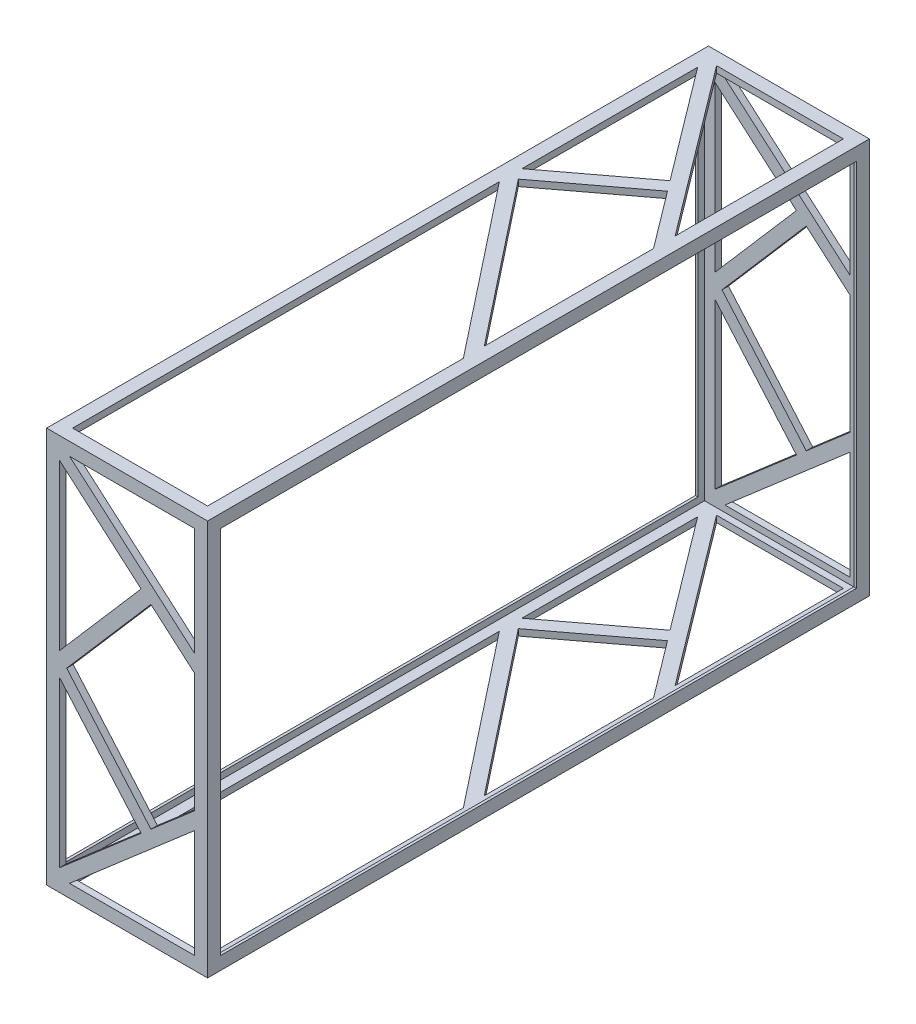
SolidWorks part; units mm, degrees
ref_plane "Front Plane" through (0, 0, 0) normal (0, 0, 1) x (1, 0, 0)
ref_plane "Top Plane" through (0, 0, 0) normal (0, 1, 0) x (1, 0, 0)
ref_plane "Right Plane" through (0, 0, 0) normal (1, 0, 0) x (0, 0, -1)
sketch "Sketch1" plane through (0, 0, 0) normal (1, 0, 0) x (0, 0, -1)
  line L0 (-5, 300) -> (505, 300)
  line L1 (0, 0) -> (500, 0)
  line L2 (0, 0) -> (0, 295)
  line L3 (0, 295) -> (500, 295)
  line L4 (500, 0) -> (500, 295)
  line L5 (505, -5) -> (505, 300)
  line L6 (-5, -5) -> (505, -5)
  line L7 (-5, -5) -> (-5, 300)
  dimension "D1" = 500
  dimension "D2" = 295
  dimension "D3" = 5
extrude "Boss-Extrude1" add sketch "Sketch1" along normal blind 120
sketch "Sketch2" plane through (120, 0, 0) normal (1, 0, 0) x (0, 0, -1)
  line L4 (-5, 300) -> (-5, -5)
  line L5 (-5, -5) -> (505, -5)
  line L6 (505, -5) -> (505, 300)
  line L7 (505, 300) -> (-5, 300)
  line L8 (-5, 300) -> (-5, -5)
  line L9 (-5, -5) -> (505, -5)
  line L10 (505, -5) -> (505, 300)
  line L11 (505, 300) -> (-5, 300)
  dimension "D1" = 0
extrude "Boss-Extrude2" add sketch "Sketch2" along normal blind 2
sketch "Sketch3" plane through (0, 0, 0) normal (-1, 0, 0) x (0, 0, 1)
  line L4 (5, -5) -> (5, 300)
  line L5 (5, 300) -> (-505, 300)
  line L6 (-505, 300) -> (-505, -5)
  line L7 (-505, -5) -> (5, -5)
  line L8 (5, -5) -> (5, 300)
  line L9 (5, 300) -> (-505, 300)
  line L10 (-505, 300) -> (-505, -5)
  line L11 (-505, -5) -> (5, -5)
  dimension "D1" = 0
extrude "Boss-Extrude3" add sketch "Sketch3" along normal blind 2
sketch "Sketch4" plane through (0, -5, 0) normal (0, -1, 0) x (1, 0, 0)
  line L0 (76.1014, -396.3181) -> (8, -345) construction
  line L1 (79.1105, -392.3249) -> (13.5822, -342.9458)
  line L2 (73.0924, -400.3113) -> (8, -351.2607)
  line L3 (79.1105, -392.3249) -> (11.0091, -341.0068) construction
  line L4 (8, -5) -> (8, -333.8778)
  line L5 (14.2607, -495) -> (112, -495)
  line L6 (112, -495) -> (112, -365.2955)
  line L7 (112, -5) -> (8, -5)
  line L8 (122, 5) -> (-2, 5)
  line L9 (-2, 5) -> (-2, -505)
  line L10 (-2, -505) -> (122, -505)
  line L11 (122, -505) -> (122, 5)
  line L12 (122, 5) -> (-2, 5)
  line L13 (-2, 5) -> (-2, -505)
  line L14 (-2, -505) -> (122, -505)
  line L15 (122, -505) -> (122, 5)
  line L16 (8, -495) -> (109.5968, -360.1764) construction
  line L17 (14.2607, -495) -> (112, -365.2955)
  line L18 (8, -486.6918) -> (73.0924, -400.3113)
  line L19 (4.0068, -491.9909) -> (105.6037, -357.1674) construction
  line L20 (11.9932, -498.0091) -> (113.59, -363.1855) construction
  line L21 (73.0924, -400.3113) -> (4.9909, -348.9932) construction
  line L22 (8, -341.9477) -> (112, -210.1957) construction
  line L23 (13.5822, -342.9458) -> (112, -218.2655)
  line L24 (8, -333.8778) -> (112, -202.1258)
  line L25 (4.0754, -338.8497) -> (108.0754, -207.0977) construction
  line L26 (11.9246, -345.0456) -> (115.9246, -213.2936) construction
  line L27 (79.1105, -392.3249) -> (112, -348.6791)
  line L28 (8, -351.2607) -> (8, -486.6918)
  line L29 (8, -5) -> (8, -495) construction
  line L30 (8, -495) -> (112, -495) construction
  line L31 (112, -348.6791) -> (112, -218.2655)
  line L32 (112, -495) -> (112, -5) construction
  line L33 (112, -202.1258) -> (112, -5)
  point P31 (112, -203.7709)
  point P34 (0, 0)
  point P36 (79.1105, -397.3249)
  dimension "D3" = 53
  dimension "D6" = 150
  dimension "D9" = 90
  dimension "D10" = 150
  dimension "D13" = 88.714
  dimension "D1" = 0
  dimension "D2" = 10
  dimension "D4" = 5
  dimension "D5" = 5
  dimension "D7" = 5
  dimension "D8" = 5
  dimension "D11" = 5
  dimension "D12" = 5
extrude "Cut-Extrude1" cut sketch "Sketch4" against normal through all contours L17 L5 L6 | L2 L28 L18 | L27 L31 L23 L1 | L24 L33 L7 L4
sketch "Sketch5" plane through (-2, 0, 0) normal (-1, 0, 0) x (0, 0, 1)
  line L0 (-495, 290) -> (-495, 5)
  line L1 (-495, 5) -> (-5, 5)
  line L2 (-5, 5) -> (-5, 290)
  line L3 (-5, 290) -> (-495, 290)
  line L4 (-505, -5) -> (5, -5)
  line L5 (5, -5) -> (5, 300)
  line L6 (5, 300) -> (-505, 300)
  line L7 (-505, 300) -> (-505, -5)
  line L8 (-505, -5) -> (5, -5)
  line L9 (5, -5) -> (5, 300)
  line L10 (5, 300) -> (-505, 300)
  line L11 (-505, 300) -> (-505, -5)
  dimension "D1" = 0
  dimension "D2" = 10
extrude "Cut-Extrude4" cut sketch "Sketch5" against normal through all contours L2 L3 L0 L1
sketch "Sketch8" plane through (0, 0, 5) normal (0, 0, 1) x (1, 0, 0)
  line L0 (8, 283.3877) -> (8, 156.4882)
  line L1 (15.6409, 5) -> (112, 5)
  line L2 (112, 5) -> (112, 88.3877)
  line L3 (112, 290) -> (15.6409, 290)
  line L4 (122, 300) -> (-2, 300)
  line L5 (-2, 300) -> (-2, -5)
  line L6 (-2, -5) -> (122, -5)
  line L7 (122, -5) -> (122, 300)
  line L8 (122, 300) -> (-2, 300)
  line L9 (-2, 300) -> (-2, -5)
  line L10 (-2, -5) -> (122, -5)
  line L11 (122, -5) -> (122, 300)
  line L12 (112, 147.5) -> (13.4463, 147.5) construction
  line L13 (74.0642, 62.1709) -> (81.6259, 68.7147) construction
  line L14 (8, 147.5) -> (-49.8667, 147.5) construction
  line L15 (15.6409, 5) -> (112, 88.3877)
  line L16 (78.354, 72.4955) -> (13.4463, 147.5)
  line L17 (8, 11.6123) -> (70.7923, 65.9518)
  line L18 (70.7923, 65.9518) -> (8, 138.5118)
  line L19 (4.7281, 8.7808) -> (108.7281, 98.7808) construction
  line L20 (11.2719, 1.2192) -> (115.2719, 91.2192) construction
  line L21 (112, 101.6123) -> (112, 193.3877)
  line L22 (112, 5) -> (112, 290) construction
  line L23 (8, 5) -> (112, 95) construction
  line L24 (8, 290) -> (8, 5) construction
  line L25 (8, 5) -> (112, 5) construction
  line L26 (8, 283.3877) -> (70.7923, 229.0482)
  line L27 (15.6409, 290) -> (112, 206.6123)
  line L28 (78.354, 222.5045) -> (112, 193.3877)
  line L29 (78.354, 72.4955) -> (112, 101.6123)
  line L30 (78.354, 222.5045) -> (13.4463, 147.5)
  line L31 (70.7923, 229.0482) -> (8, 156.4882)
  line L32 (8, 138.5118) -> (8, 11.6123)
  line L33 (112, 290) -> (8, 290) construction
  line L34 (112, 206.6123) -> (112, 290)
  point P13 (112, 95.9654)
  point P22 (112, 102.6812)
  dimension "D1" = 0
  dimension "D2" = 10
  dimension "D3" = 5
  dimension "D4" = 5
extrude "Cut-Extrude5" cut sketch "Sketch8" against normal through all contours L15 L1 L2 | L18 L32 L17 | L28 L30 L16 L29 L21 | L31 L26 L0 | L27 L34 L3
